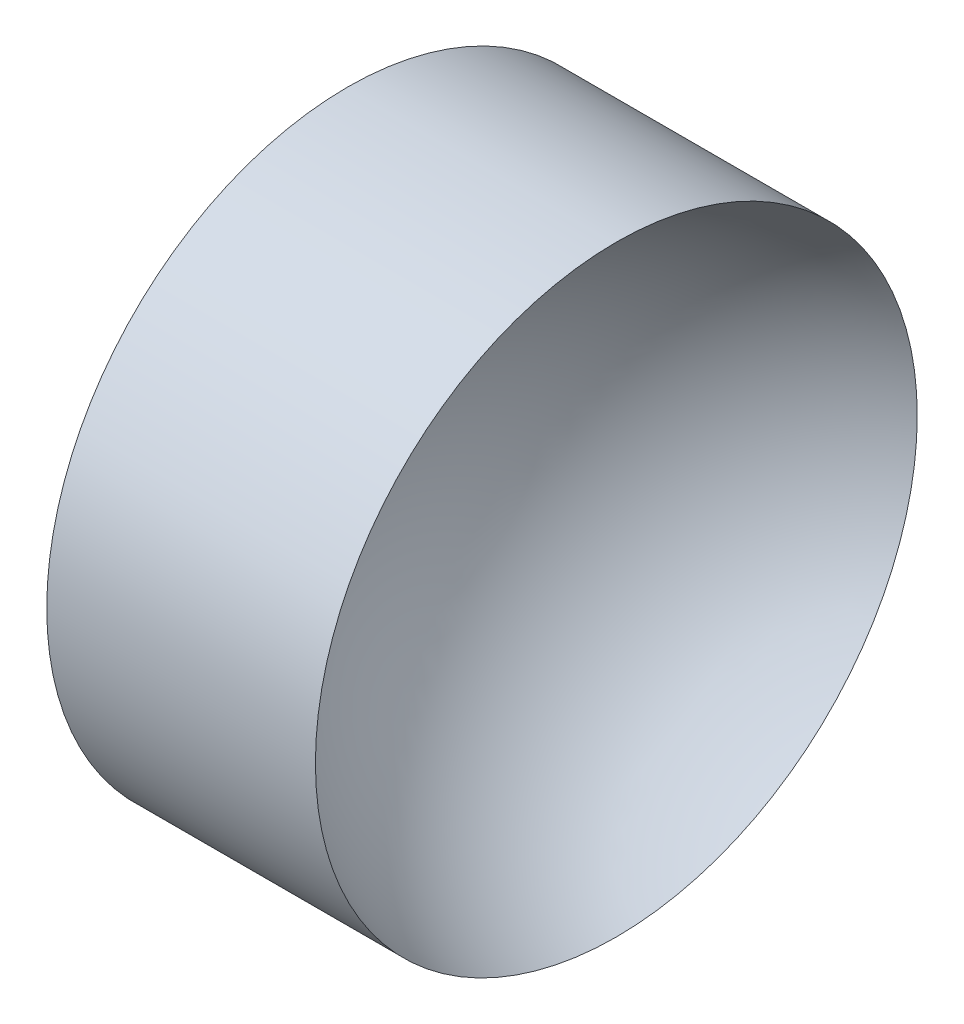
SolidWorks part; units mm, degrees
ref_plane "前视基准面" through (0, 0, 0) normal (0, 0, 1) x (1, 0, 0)
ref_plane "上视基准面" through (0, 0, 0) normal (0, 1, 0) x (1, 0, 0)
ref_plane "右视基准面" through (0, 0, 0) normal (1, 0, 0) x (0, 0, -1)
sketch "草图1" plane through (0, 0, 0) normal (0, 0, 1) x (1, 0, 0)
  line L0 (56.1009, 32.6108) -> (68.2773, 32.6108) construction
  line L1 (57.5323, 32.6108) -> (57.5323, 45.1108)
  line L2 (57.5323, 45.1108) -> (68.6923, 45.1108)
  line L3 (59.5323, 32.6108) -> (57.5323, 32.6108)
  arc A0 (68.6923, 45.1108) -> (59.5323, 32.6108) centre (72.6413, 32.6108) ccw
revolve "旋转1" add sketch "草图1" angle 360 about L0
